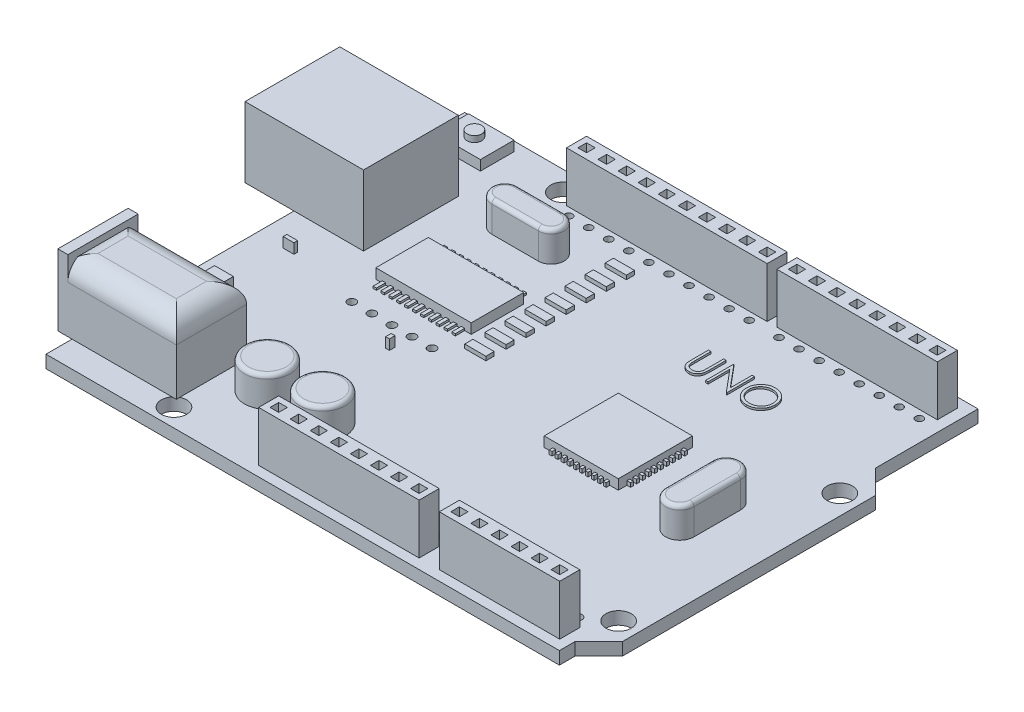
SolidWorks part; units mm, degrees
ref_plane "Front Plane" through (0, 0, 0) normal (0, 0, 1) x (1, 0, 0)
ref_plane "Top Plane" through (0, 0, 0) normal (0, 1, 0) x (1, 0, 0)
ref_plane "Right Plane" through (0, 0, 0) normal (1, 0, 0) x (0, 0, -1)
sketch "Sketch2" plane through (0, 0, 0) normal (0, 1, 0) x (1, 0, 0)
  line L0 (0, 0) -> (65, 0)
  line L1 (0, 0) -> (0, -53)
  line L2 (65, 0) -> (65, -13)
  line L3 (0, -53) -> (65, -53)
  line L4 (65, -13) -> (68, -16)
  line L5 (68, -16) -> (68, -48)
  line L6 (68, -48) -> (65, -51)
  line L7 (65, -51) -> (65, -53)
  circle A0 centre (15, -2.5) radius 1.6
  circle A1 centre (65.5, -18) radius 1.6
  circle A2 centre (65.5, -46) radius 1.6
  circle A3 centre (13.9, -50.7) radius 1.6
  dimension "D8" = 3.2
  dimension "D9" = 15
  dimension "D12" = 35
  dimension "D13" = 50.5
  dimension "D14" = 1.1
  dimension "D15" = 4.7
  dimension "D1" = 65
  dimension "D2" = 53
  dimension "D3" = 37
  dimension "D4" = 40
  dimension "D5" = 2
  dimension "D6" = 5
  dimension "D7" = 68
  dimension "D10" = 65.5
  dimension "D11" = 7
extrude "Boss-Extrude1" add sketch "Sketch2" along normal blind 1.6
sketch "Sketch3" plane through (0, 1.6, 0) normal (0, 1, 0) x (1, 0, 0)
  line L0 (-6.2, -9.6) -> (8.8, -9.6)
  line L1 (-6.2, -9.6) -> (-6.2, -21.6)
  line L2 (8.8, -9.6) -> (8.8, -21.6)
  line L3 (-6.2, -21.6) -> (8.8, -21.6)
  line L4 (65, 0) -> (0, 0) construction
  line L5 (0, 0) -> (0, -53) construction
  dimension "D1" = 9.6
  dimension "D2" = 12
  dimension "D3" = 15
  dimension "D4" = 6.2
extrude "Boss-Extrude2" add sketch "Sketch3" along normal blind 8.9
sketch "Sketch5" plane through (0, 1.6, 0) normal (0, 1, 0) x (1, 0, 0)
  line L0 (0, 0) -> (0, -9.6) construction
  line L1 (7.4283, -5.4315) -> (1.6434, -5.4315)
  line L2 (7.4283, -5.4315) -> (7.4283, -1.1571)
  line L3 (7.4283, -1.1571) -> (1.6434, -1.1571)
  line L4 (1.6434, -5.4315) -> (1.6434, -1.1571)
  line L5 (7.4283, -5.4315) -> (1.6434, -1.1571) construction
  line L6 (7.4283, -1.1571) -> (1.6434, -5.4315) construction
  line L7 (65, 0) -> (0, 0) construction
  point P0 (4.5358, -3.2943)
  dimension "D1" = 4.2744
  dimension "D2" = 5.7848
  dimension "D3" = 1.6434
  dimension "D4" = 1.1571
extrude "Boss-Extrude3" add sketch "Sketch5" along normal blind 1.27
sketch "Sketch6" plane through (0, 2.87, 0) normal (0, 1, 0) x (1, 0, 0)
  line L0 (1.6434, -1.1571) -> (7.4283, -5.4315) construction
  circle A0 centre (4.5358, -3.2943) radius 0.9278
  dimension "D1" = 1.8555
extrude "Boss-Extrude4" add sketch "Sketch6" along normal blind 0.762
sketch "Sketch7" plane through (0, 1.6, 0) normal (0, 1, 0) x (1, 0, 0)
  line L0 (0, -21.6) -> (0, -53) construction
  line L1 (-1.8, -40.8) -> (13.2, -40.8)
  line L2 (-1.8, -40.8) -> (-1.8, -49.7)
  line L3 (-1.8, -49.7) -> (13.2, -49.7)
  line L4 (13.2, -40.8) -> (13.2, -49.7)
  line L5 (-1.8, -40.8) -> (13.2, -49.7) construction
  line L6 (-1.8, -49.7) -> (13.2, -40.8) construction
  line L7 (0, -53) -> (65, -53) construction
  point P0 (5.7, -45.25)
  dimension "D1" = 8.9
  dimension "D2" = 1.8
  dimension "D3" = 15
  dimension "D4" = 3.3
extrude "Boss-Extrude5" add sketch "Sketch7" along normal blind 8.5
fillet "Fillet1" radius 2.54 4 edges at (5.7, 10.1, 49.7) (-1.8, 10.1, 45.25) (5.7, 10.1, 40.8) (13.2, 10.1, 45.25)
sketch "Sketch8" plane through (-1.8, 0, 0) normal (-1, 0, 0) x (0, 0, 1)
  line L0 (49.7, 1.6) -> (53, 1.6) construction
  line L1 (49.7, 1.6) -> (40.8, 1.6)
  line L2 (49.7, 1.6) -> (49.7, 10.6)
  line L3 (49.7, 10.6) -> (40.8, 10.6)
  line L4 (40.8, 1.6) -> (40.8, 10.6)
  line L5 (49.7, 1.6) -> (40.8, 10.6) construction
  line L6 (49.7, 10.6) -> (40.8, 1.6) construction
  line L7 (49.7, 7.56) -> (49.7, 1.6) construction
  line L9 (40.8, 7.56) -> (40.8, 1.6) construction
  point P0 (45.25, 6.1)
  dimension "D1" = 9
extrude "Boss-Extrude6" add sketch "Sketch8" against normal blind 1.27
sketch "Sketch9" plane through (-1.8, 0, 0) normal (-1, 0, 0) x (0, 0, 1)
  line L0 (45.25, 10.6) -> (45.25, 1.6) construction
  line L1 (49.7, 10.6) -> (40.8, 10.6) construction
  line L2 (40.8, 1.6) -> (49.7, 1.6) construction
  circle A0 centre (45.25, 6.1) radius 3
  dimension "D1" = 6
extrude "Cut-Extrude2" cut sketch "Sketch9" against normal blind 8.89
sketch "Sketch11" plane through (0, 1.6, 0) normal (0, 1, 0) x (1, 0, 0)
  line L0 (15.083, -10) -> (20.9573, -10) construction
  line L1 (15.083, -8.3682) -> (20.9573, -8.3682)
  line L2 (15.083, -11.6318) -> (20.9573, -11.6318)
  line L3 (59.2606, -32.0122) -> (59.2606, -26.1378) construction
  line L4 (57.4656, -32.0122) -> (57.4656, -26.1378)
  line L5 (61.0555, -32.0122) -> (61.0555, -26.1378)
  line L6 (0, -53) -> (65, -53) construction
  line L7 (0, -21.6) -> (0, -40.8) construction
  line L8 (65, 0) -> (0, 0) construction
  circle A0 centre (18.0202, -43) radius 2.8915
  circle A1 centre (25.0202, -43) radius 2.8915
  arc A2 (15.083, -8.3682) -> (15.083, -11.6318) centre (15.083, -10) ccw
  arc A3 (20.9573, -11.6318) -> (20.9573, -8.3682) centre (20.9573, -10) ccw
  arc A4 (57.4656, -32.0122) -> (61.0555, -32.0122) centre (59.2606, -32.0122) ccw
  arc A5 (61.0555, -26.1378) -> (57.4656, -26.1378) centre (59.2606, -26.1378) ccw
  point P6 (18.0202, -10)
  point P11 (59.2606, -29.075)
  dimension "D1" = 7
  dimension "D2" = 5.783
  dimension "D4" = 18.0202
  dimension "D6" = 1.6318
  dimension "14" = 10
  dimension "D5" = 5.8744
  dimension "D7" = 10
  dimension "D8" = 18.0202
extrude "Boss-Extrude8" add sketch "Sketch11" along normal blind 3.81
fillet "Fillet2" radius 0.508 1 edges at (18.0202, 5.41, 45.8915)
fillet "Fillet3" radius 0.508 9 edges at (59.2606, 5.41, 24.3429) (61.0555, 5.41, 29.075) (59.2606, 5.41, 33.8071) (18.0202, 5.41, 8.3682) (22.5891, 5.41, 10) (18.0202, 5.41, 11.6318) (57.4656, 5.41, 29.075) (13.4512, 5.41, 10) (25.0202, 5.41, 45.8915)
sketch "Sketch12" plane through (0, 1.6, 0) normal (0, 1, 0) x (1, 0, 0)
  line L0 (39.53, -1.23) -> (39.53, -3.77) construction
  line L1 (16.67, -1.23) -> (42.07, -1.23)
  line L2 (16.67, -1.23) -> (16.67, -3.77)
  line L3 (16.67, -3.77) -> (42.07, -3.77)
  line L4 (42.07, -1.23) -> (42.07, -3.77)
  line L5 (16.67, -1.23) -> (42.07, -3.77) construction
  line L6 (16.67, -3.77) -> (42.07, -1.23) construction
  line L7 (43.3, -1.23) -> (63.62, -1.23)
  line L8 (43.3, -1.23) -> (43.3, -3.77)
  line L9 (43.3, -3.77) -> (63.62, -3.77)
  line L10 (63.62, -1.23) -> (63.62, -3.77)
  line L11 (43.3, -1.23) -> (63.62, -3.77) construction
  line L12 (43.3, -3.77) -> (63.62, -1.23) construction
  line L13 (39.53, -1.23) -> (42.07, -3.77) construction
  line L14 (0, 0) -> (0, -9.6) construction
  line L15 (16.67, -2.5) -> (15, -2.5) construction
  line L17 (25.65, -49.19) -> (45.97, -49.19)
  line L18 (25.65, -49.19) -> (25.65, -51.73)
  line L19 (25.65, -51.73) -> (45.97, -51.73)
  line L20 (45.97, -49.19) -> (45.97, -51.73)
  line L21 (48.53, -49.19) -> (63.77, -49.19)
  line L22 (48.53, -49.19) -> (48.53, -51.73)
  line L23 (48.53, -51.73) -> (63.77, -51.73)
  line L24 (63.77, -49.19) -> (63.77, -51.73)
  line L25 (43.43, -49.19) -> (43.43, -51.73) construction
  line L26 (43.43, -51.73) -> (45.97, -49.19) construction
  line L27 (0, -49.7) -> (0, -53) construction
  line L28 (0, -53) -> (65, -53) construction
  line L29 (63.77, -49.19) -> (61.23, -51.73) construction
  line L30 (63.62, -1.23) -> (61.38, -3.77) construction
  circle A0 centre (15, -2.5) radius 1.6 construction
  point P0 (29.37, -2.5)
  point P5 (53.46, -2.5)
  point P14 (40.8, -2.5)
  point P27 (45.97, -50.46)
  point P28 (44.7, -50.46)
  point P35 (62.5, -50.46)
  point P37 (62.5, -2.5)
  dimension "D1" = 25.4
  dimension "D2" = 2.54
  dimension "D3" = 2.54
  dimension "D4" = 40.8
  dimension "D5" = 20.32
  dimension "D6" = 2.54
  dimension "D7" = 44.7
  dimension "D8" = 2.54
  dimension "D9" = 2.54
  dimension "D10" = 62.5
  dimension "D11" = 2.24
  dimension "D12" = 62.5
  dimension "D13" = 20.32
  dimension "D14" = 15.24
extrude "Boss-Extrude9" add sketch "Sketch12" along normal blind 6.35
sketch "Sketch13" plane through (0, 7.95, 0) normal (0, 1, 0) x (1, 0, 0)
  line L0 (19.9337, -3.0463) -> (19.9337, -1.9537)
  line L1 (18.4863, -3.0463) -> (17.3937, -3.0463)
  line L2 (18.4863, -3.0463) -> (18.4863, -1.9537)
  line L3 (18.4863, -1.9537) -> (17.3937, -1.9537)
  line L4 (17.3937, -3.0463) -> (17.3937, -1.9537)
  line L5 (18.4863, -3.0463) -> (17.3937, -1.9537) construction
  line L6 (18.4863, -1.9537) -> (17.3937, -3.0463) construction
  line L7 (21.0263, -1.9537) -> (19.9337, -1.9537)
  line L8 (21.0263, -3.0463) -> (19.9337, -3.0463)
  line L9 (21.0263, -3.0463) -> (21.0263, -1.9537)
  line L10 (22.4737, -3.0463) -> (22.4737, -1.9537)
  line L11 (23.5663, -1.9537) -> (22.4737, -1.9537)
  line L12 (23.5663, -3.0463) -> (22.4737, -3.0463)
  line L13 (23.5663, -3.0463) -> (23.5663, -1.9537)
  line L14 (25.0137, -3.0463) -> (25.0137, -1.9537)
  line L15 (26.1063, -1.9537) -> (25.0137, -1.9537)
  line L16 (26.1063, -3.0463) -> (25.0137, -3.0463)
  line L17 (26.1063, -3.0463) -> (26.1063, -1.9537)
  line L18 (27.5537, -3.0463) -> (27.5537, -1.9537)
  line L19 (28.6463, -1.9537) -> (27.5537, -1.9537)
  line L20 (28.6463, -3.0463) -> (27.5537, -3.0463)
  line L21 (28.6463, -3.0463) -> (28.6463, -1.9537)
  line L22 (30.0937, -3.0463) -> (30.0937, -1.9537)
  line L23 (31.1863, -1.9537) -> (30.0937, -1.9537)
  line L24 (31.1863, -3.0463) -> (30.0937, -3.0463)
  line L25 (31.1863, -3.0463) -> (31.1863, -1.9537)
  line L26 (32.6337, -3.0463) -> (32.6337, -1.9537)
  line L27 (33.7263, -1.9537) -> (32.6337, -1.9537)
  line L28 (33.7263, -3.0463) -> (32.6337, -3.0463)
  line L29 (33.7263, -3.0463) -> (33.7263, -1.9537)
  line L30 (35.1737, -3.0463) -> (35.1737, -1.9537)
  line L31 (36.2663, -1.9537) -> (35.1737, -1.9537)
  line L32 (36.2663, -3.0463) -> (35.1737, -3.0463)
  line L33 (36.2663, -3.0463) -> (36.2663, -1.9537)
  line L34 (16.67, -2.5) -> (17.94, -2.5) construction
  line L35 (16.67, -1.23) -> (16.67, -3.77) construction
  line L36 (42.07, -1.23) -> (43.3, -1.23) construction
  line L37 (43.3, -1.23) -> (42.685, -1.23) construction
  line L38 (42.685, -1.23) -> (42.685, 0) construction
  line L39 (65, 0) -> (0, 0) construction
  line L40 (44.0237, -3.0463) -> (44.0237, -1.9537)
  line L41 (44.0237, -3.0463) -> (45.1163, -3.0463)
  line L42 (44.0237, -1.9537) -> (45.1163, -1.9537)
  line L43 (49.1037, -3.0463) -> (49.1037, -1.9537)
  line L44 (49.1037, -3.0463) -> (50.1963, -3.0463)
  line L45 (49.1037, -1.9537) -> (50.1963, -1.9537)
  line L46 (50.1963, -3.0463) -> (50.1963, -1.9537)
  line L47 (51.6437, -3.0463) -> (51.6437, -1.9537)
  line L48 (51.6437, -3.0463) -> (52.7363, -3.0463)
  line L49 (51.6437, -1.9537) -> (52.7363, -1.9537)
  line L50 (52.7363, -3.0463) -> (52.7363, -1.9537)
  line L51 (54.1837, -3.0463) -> (54.1837, -1.9537)
  line L52 (54.1837, -3.0463) -> (55.2763, -3.0463)
  line L53 (54.1837, -1.9537) -> (55.2763, -1.9537)
  line L54 (55.2763, -3.0463) -> (55.2763, -1.9537)
  line L55 (56.7237, -3.0463) -> (56.7237, -1.9537)
  line L56 (56.7237, -3.0463) -> (57.8163, -3.0463)
  line L57 (56.7237, -1.9537) -> (57.8163, -1.9537)
  line L58 (57.8163, -3.0463) -> (57.8163, -1.9537)
  line L59 (59.2637, -3.0463) -> (59.2637, -1.9537)
  line L60 (59.2637, -3.0463) -> (60.3563, -3.0463)
  line L61 (59.2637, -1.9537) -> (60.3563, -1.9537)
  line L62 (60.3563, -3.0463) -> (60.3563, -1.9537)
  line L63 (61.8037, -3.0463) -> (61.8037, -1.9537)
  line L64 (61.8037, -3.0463) -> (62.8963, -3.0463)
  line L65 (61.8037, -1.9537) -> (62.8963, -1.9537)
  line L66 (62.8963, -3.0463) -> (62.8963, -1.9537)
  line L67 (45.1163, -3.0463) -> (45.1163, -1.9537)
  line L68 (46.5637, -3.0463) -> (46.5637, -1.9537)
  line L69 (46.5637, -3.0463) -> (47.6563, -3.0463)
  line L71 (46.5637, -1.9537) -> (47.6563, -1.9537)
  line L72 (47.6563, -3.0463) -> (47.6563, -1.9537)
  line L73 (41.6137, -49.9137) -> (42.7063, -49.9137)
  line L74 (41.6137, -49.9137) -> (41.6137, -51.0063)
  line L75 (41.6137, -51.0063) -> (42.7063, -51.0063)
  line L77 (26.3737, -49.9137) -> (27.4663, -49.9137)
  line L78 (26.3737, -49.9137) -> (26.3737, -51.0063)
  line L79 (26.3737, -51.0063) -> (27.4663, -51.0063)
  line L80 (27.4663, -49.9137) -> (27.4663, -51.0063)
  line L81 (26.3737, -50.46) -> (25.65, -50.46) construction
  line L82 (25.65, -49.19) -> (25.65, -51.73) construction
  line L83 (28.9137, -49.9137) -> (30.0063, -49.9137)
  line L84 (28.9137, -49.9137) -> (28.9137, -51.0063)
  line L85 (28.9137, -51.0063) -> (30.0063, -51.0063)
  line L86 (30.0063, -49.9137) -> (30.0063, -51.0063)
  line L87 (31.4537, -49.9137) -> (32.5463, -49.9137)
  line L88 (31.4537, -49.9137) -> (31.4537, -51.0063)
  line L89 (31.4537, -51.0063) -> (32.5463, -51.0063)
  line L90 (32.5463, -49.9137) -> (32.5463, -51.0063)
  line L91 (33.9937, -49.9137) -> (35.0863, -49.9137)
  line L92 (33.9937, -49.9137) -> (33.9937, -51.0063)
  line L93 (33.9937, -51.0063) -> (35.0863, -51.0063)
  line L94 (35.0863, -49.9137) -> (35.0863, -51.0063)
  line L95 (36.5337, -49.9137) -> (37.6263, -49.9137)
  line L96 (36.5337, -49.9137) -> (36.5337, -51.0063)
  line L97 (36.5337, -51.0063) -> (37.6263, -51.0063)
  line L98 (37.6263, -49.9137) -> (37.6263, -51.0063)
  line L99 (39.0737, -49.9137) -> (40.1663, -49.9137)
  line L100 (39.0737, -49.9137) -> (39.0737, -51.0063)
  line L101 (39.0737, -51.0063) -> (40.1663, -51.0063)
  line L102 (40.1663, -49.9137) -> (40.1663, -51.0063)
  line L103 (45.97, -51.73) -> (48.53, -51.73) construction
  line L104 (48.53, -51.73) -> (47.25, -51.73) construction
  line L105 (47.25, -51.73) -> (47.25, -53) construction
  line L106 (0, -53) -> (65, -53) construction
  line L107 (49.2537, -49.9137) -> (49.2537, -51.0063)
  line L108 (54.3337, -49.9137) -> (54.3337, -51.0063)
  line L109 (55.4263, -51.0063) -> (54.3337, -51.0063)
  line L110 (55.4263, -49.9137) -> (55.4263, -51.0063)
  line L111 (55.4263, -49.9137) -> (54.3337, -49.9137)
  line L112 (56.8737, -49.9137) -> (56.8737, -51.0063)
  line L113 (57.9663, -51.0063) -> (56.8737, -51.0063)
  line L114 (57.9663, -49.9137) -> (57.9663, -51.0063)
  line L115 (57.9663, -49.9137) -> (56.8737, -49.9137)
  line L116 (59.4137, -49.9137) -> (59.4137, -51.0063)
  line L117 (60.5063, -51.0063) -> (59.4137, -51.0063)
  line L118 (60.5063, -49.9137) -> (60.5063, -51.0063)
  line L119 (60.5063, -49.9137) -> (59.4137, -49.9137)
  line L120 (61.9537, -49.9137) -> (61.9537, -51.0063)
  line L121 (63.0463, -51.0063) -> (61.9537, -51.0063)
  line L122 (63.0463, -49.9137) -> (63.0463, -51.0063)
  line L123 (63.0463, -49.9137) -> (61.9537, -49.9137)
  line L124 (50.3463, -51.0063) -> (49.2537, -51.0063)
  line L125 (50.3463, -49.9137) -> (50.3463, -51.0063)
  line L126 (50.3463, -49.9137) -> (49.2537, -49.9137)
  line L127 (51.7937, -49.9137) -> (51.7937, -51.0063)
  line L128 (52.8863, -51.0063) -> (51.7937, -51.0063)
  line L129 (52.8863, -49.9137) -> (52.8863, -51.0063)
  line L130 (52.8863, -49.9137) -> (51.7937, -49.9137)
  line L132 (37.7137, -3.0463) -> (37.7137, -1.9537)
  line L133 (38.8063, -1.9537) -> (37.7137, -1.9537)
  line L134 (38.8063, -3.0463) -> (37.7137, -3.0463)
  line L135 (38.8063, -3.0463) -> (38.8063, -1.9537)
  line L136 (40.2537, -3.0463) -> (40.2537, -1.9537)
  line L137 (41.3463, -1.9537) -> (40.2537, -1.9537)
  line L138 (41.3463, -3.0463) -> (40.2537, -3.0463)
  line L139 (41.3463, -3.0463) -> (41.3463, -1.9537)
  line L140 (42.7063, -49.9137) -> (42.7063, -51.0063)
  line L141 (44.1537, -49.9137) -> (45.2463, -49.9137)
  line L142 (44.1537, -49.9137) -> (44.1537, -51.0063)
  line L143 (44.1537, -51.0063) -> (45.2463, -51.0063)
  line L144 (45.2463, -49.9137) -> (45.2463, -51.0063)
  point P0 (17.94, -2.5)
  point P84 (26.92, -51.0063)
  dimension "D2" = 2.54
  dimension "D3" = 1.0927
  dimension "D4" = 1.27
  dimension "D5" = 1.27
  dimension "D6" = 8
  dimension "D7" = 2.54
  dimension "D1" = 10
extrude "Cut-Extrude3" cut sketch "Sketch13" against normal blind 3.81
sketch "Sketch15" plane through (0, 1.6, 0) normal (0, 1, 0) x (1, 0, 0)
  line L0 (0, -53) -> (65, -53) construction
  line L1 (51.1538, -31.6917) -> (41.7703, -31.6917)
  line L2 (51.1538, -31.6917) -> (51.1538, -22.3083)
  line L3 (51.1538, -22.3083) -> (41.7703, -22.3083)
  line L4 (41.7703, -31.6917) -> (41.7703, -22.3083)
  line L5 (51.1538, -31.6917) -> (41.7703, -22.3083) construction
  line L6 (51.1538, -22.3083) -> (41.7703, -31.6917) construction
  line L7 (4.7493, -26.358) -> (3.3785, -26.358)
  line L8 (4.7493, -26.358) -> (4.7493, -25.8868)
  line L9 (4.7493, -25.8868) -> (3.3785, -25.8868)
  line L10 (3.3785, -26.358) -> (3.3785, -25.8868)
  line L11 (4.7493, -26.358) -> (3.3785, -25.8868) construction
  line L12 (4.7493, -25.8868) -> (3.3785, -26.358) construction
  line L13 (21.3282, -30.8535) -> (20.8488, -30.8535)
  line L14 (21.3282, -30.8535) -> (21.3282, -30.1486)
  line L15 (21.3282, -30.1486) -> (20.8488, -30.1486)
  line L16 (20.8488, -30.8535) -> (20.8488, -30.1486)
  line L17 (21.3282, -30.8535) -> (20.8488, -30.1486) construction
  line L18 (21.3282, -30.1486) -> (20.8488, -30.8535) construction
  line L19 (4.6108, -37.8097) -> (2.2268, -37.8097)
  line L20 (4.6108, -37.8097) -> (4.6108, -33.8836)
  line L21 (4.6108, -33.8836) -> (2.2268, -33.8836)
  line L22 (2.2268, -37.8097) -> (2.2268, -33.8836)
  line L23 (4.6108, -37.8097) -> (2.2268, -33.8836) construction
  line L24 (4.6108, -33.8836) -> (2.2268, -37.8097) construction
  line L25 (24.7492, -23.9138) -> (12.6715, -23.9138)
  line L26 (24.7492, -23.9138) -> (24.7492, -17.271)
  line L27 (24.7492, -17.271) -> (12.6715, -17.271)
  line L28 (12.6715, -23.9138) -> (12.6715, -17.271)
  line L29 (24.7492, -23.9138) -> (12.6715, -17.271) construction
  line L30 (24.7492, -17.271) -> (12.6715, -23.9138) construction
  line L31 (68, -48) -> (68, -16) construction
  line L32 (0, -21.6) -> (0, -40.8) construction
  line L34 (65, 0) -> (0, 0) construction
  point P0 (46.4621, -27)
  point P5 (4.0639, -26.1224)
  point P10 (21.0885, -30.501)
  point P15 (3.4188, -35.8466)
  point P20 (18.7104, -20.5924)
  dimension "D1" = 9.3835
  dimension "D2" = 12.0778
  dimension "D3" = 6.6428
  dimension "D4" = 26
  dimension "D5" = 21.5379
  dimension "D6" = 18.7104
  dimension "D7" = 20.5924
extrude "Boss-Extrude10" add sketch "Sketch15" along normal blind 1.27
sketch "Sketch16" plane through (0, 1.6, 0) normal (0, 1, 0) x (1, 0, 0)
  line L0 (17.94, -3.0463) -> (17.94, -4.77) construction
  line L1 (17.3937, -3.0463) -> (18.4863, -3.0463) construction
  line L2 (16.67, -3.77) -> (42.07, -3.77) construction
  line L3 (40.8, -3.0463) -> (40.8, -4.77) construction
  line L4 (40.2537, -3.0463) -> (41.3463, -3.0463) construction
  line L5 (42.07, -1.23) -> (43.3, -1.23) construction
  line L6 (43.3, -1.23) -> (42.685, -1.23) construction
  line L7 (42.685, -1.23) -> (42.685, 0) construction
  line L8 (65, 0) -> (0, 0) construction
  line L9 (44.57, -3.0463) -> (44.57, -4.77) construction
  circle A0 centre (-9.9058, 11.1483) radius 1.2565
  circle A1 centre (30.64, -4.77) radius 0.4778
  circle A2 centre (33.18, -4.77) radius 0.4778
  circle A3 centre (17.94, -4.77) radius 0.4778
  circle A4 centre (20.48, -4.77) radius 0.4778
  circle A5 centre (23.02, -4.77) radius 0.4778
  circle A6 centre (25.56, -4.77) radius 0.4778
  circle A7 centre (28.1, -4.77) radius 0.4778
  circle A8 centre (35.72, -4.77) radius 0.4778
  circle A9 centre (38.26, -4.77) radius 0.4778
  circle A10 centre (40.8, -4.77) radius 0.4778
  circle A11 centre (44.57, -4.77) radius 0.4778
  circle A12 centre (47.11, -4.77) radius 0.4778
  circle A13 centre (49.65, -4.77) radius 0.4778
  circle A14 centre (57.27, -4.77) radius 0.4778
  circle A15 centre (59.81, -4.77) radius 0.4778
  circle A16 centre (62.35, -4.77) radius 0.4778
  circle A19 centre (52.19, -4.77) radius 0.4778
  circle A20 centre (54.73, -4.77) radius 0.4778
  dimension "D4" = 0.9556
  dimension "D2" = 2.54
  dimension "D3" = 1
  dimension "D1" = 10
extrude "Cut-Extrude5" cut sketch "Sketch16" against normal blind 3.81
sketch "Sketch17" plane through (0, 1.6, 0) normal (0, 1, 0) x (1, 0, 0)
  line L0 (28.5824, -23.3444) -> (25.9009, -22.3015) construction
  line L1 (28.5824, -25.8844) -> (25.9009, -25.8844)
  line L2 (28.5824, -25.8844) -> (28.5824, -24.8415)
  line L3 (28.5824, -24.8415) -> (25.9009, -24.8415)
  line L4 (25.9009, -25.8844) -> (25.9009, -24.8415)
  line L5 (28.5824, -25.8844) -> (25.9009, -24.8415) construction
  line L6 (28.5824, -24.8415) -> (25.9009, -25.8844) construction
  line L7 (28.5824, -22.3015) -> (25.9009, -23.3444) construction
  line L8 (28.5824, -23.3444) -> (28.5824, -22.3015)
  line L9 (28.5824, -23.3444) -> (25.9009, -23.3444)
  line L10 (25.9009, -23.3444) -> (25.9009, -22.3015)
  line L11 (28.5824, -22.3015) -> (25.9009, -22.3015)
  line L12 (28.5824, -20.8044) -> (25.9009, -19.7615) construction
  line L13 (28.5824, -19.7615) -> (25.9009, -20.8044) construction
  line L14 (28.5824, -20.8044) -> (28.5824, -19.7615)
  line L15 (28.5824, -20.8044) -> (25.9009, -20.8044)
  line L16 (25.9009, -20.8044) -> (25.9009, -19.7615)
  line L17 (28.5824, -19.7615) -> (25.9009, -19.7615)
  line L18 (28.5824, -18.2644) -> (25.9009, -17.2215) construction
  line L19 (28.5824, -17.2215) -> (25.9009, -18.2644) construction
  line L20 (28.5824, -18.2644) -> (28.5824, -17.2215)
  line L21 (28.5824, -18.2644) -> (25.9009, -18.2644)
  line L22 (25.9009, -18.2644) -> (25.9009, -17.2215)
  line L23 (28.5824, -17.2215) -> (25.9009, -17.2215)
  line L24 (28.5824, -15.7244) -> (25.9009, -14.6815) construction
  line L25 (28.5824, -14.6815) -> (25.9009, -15.7244) construction
  line L26 (28.5824, -15.7244) -> (28.5824, -14.6815)
  line L27 (28.5824, -15.7244) -> (25.9009, -15.7244)
  line L28 (25.9009, -15.7244) -> (25.9009, -14.6815)
  line L29 (28.5824, -14.6815) -> (25.9009, -14.6815)
  line L30 (28.5824, -13.1844) -> (25.9009, -12.1415) construction
  line L31 (28.5824, -12.1415) -> (25.9009, -13.1844) construction
  line L32 (28.5824, -13.1844) -> (28.5824, -12.1415)
  line L33 (28.5824, -13.1844) -> (25.9009, -13.1844)
  line L34 (25.9009, -13.1844) -> (25.9009, -12.1415)
  line L35 (28.5824, -12.1415) -> (25.9009, -12.1415)
  line L36 (28.5824, -10.6444) -> (25.9009, -9.6015) construction
  line L37 (28.5824, -9.6015) -> (25.9009, -10.6444) construction
  line L38 (28.5824, -10.6444) -> (28.5824, -9.6015)
  line L39 (28.5824, -10.6444) -> (25.9009, -10.6444)
  line L40 (25.9009, -10.6444) -> (25.9009, -9.6015)
  line L41 (28.5824, -9.6015) -> (25.9009, -9.6015)
  line L42 (28.5824, -8.1044) -> (25.9009, -7.0615) construction
  line L43 (28.5824, -7.0615) -> (25.9009, -8.1044) construction
  line L44 (28.5824, -8.1044) -> (28.5824, -7.0615)
  line L45 (28.5824, -8.1044) -> (25.9009, -8.1044)
  line L46 (25.9009, -8.1044) -> (25.9009, -7.0615)
  line L47 (28.5824, -7.0615) -> (25.9009, -7.0615)
  point P0 (27.2416, -25.363)
  point P6 (27.2416, -22.823)
  point P12 (27.2416, -20.283)
  point P17 (27.2416, -17.743)
  point P22 (27.2416, -15.203)
  point P27 (27.2416, -12.663)
  point P32 (27.2416, -10.123)
  point P37 (27.2416, -7.583)
  dimension "D2" = 1.0429
  dimension "D3" = 2.54
  dimension "D1" = 8
extrude "Boss-Extrude11" add sketch "Sketch17" along normal blind 0.508
sketch "Sketch18" plane through (0, 1.6, 0) normal (0, 1, 0) x (1, 0, 0)
  text T0 "UNO"
sketch "Sketch20" plane through (0, 1.6, 0) normal (0, 1, 0) x (1, 0, 0)
  line L0 (45.97, -49.19) -> (25.65, -49.19) construction
  line L1 (26.92, -48.19) -> (26.92, -49.9137) construction
  line L2 (27.4663, -49.9137) -> (26.3737, -49.9137) construction
  line L3 (45.97, -51.73) -> (48.53, -51.73) construction
  line L4 (48.53, -51.73) -> (47.25, -51.73) construction
  line L5 (47.25, -51.73) -> (47.25, -53) construction
  line L6 (0, -53) -> (65, -53) construction
  circle A0 centre (26.92, -48.19) radius 0.5676
  circle A1 centre (29.46, -48.19) radius 0.5676
  circle A2 centre (32, -48.19) radius 0.5676
  circle A3 centre (34.54, -48.19) radius 0.5676
  circle A4 centre (37.08, -48.19) radius 0.5676
  circle A5 centre (39.62, -48.19) radius 0.5676
  circle A6 centre (42.16, -48.19) radius 0.5676
  circle A7 centre (44.7, -48.19) radius 0.5676
  circle A8 centre (49.8, -48.19) radius 0.5676
  circle A9 centre (52.34, -48.19) radius 0.5676
  circle A10 centre (54.88, -48.19) radius 0.5676
  circle A11 centre (57.42, -48.19) radius 0.5676
  circle A12 centre (59.96, -48.19) radius 0.5676
  circle A13 centre (62.5, -48.19) radius 0.5676
  dimension "D1" = 8
  dimension "D2" = 1.1352
  dimension "D3" = 2.54
  dimension "D4" = 1
extrude "Cut-Extrude6" cut sketch "Sketch20" against normal blind 23.368
sketch "Sketch21" plane through (0, 1.6, 0) normal (0, 1, 0) x (1, 0, 0)
  line L0 (18.7104, -23.9138) -> (18.7104, -27.9138) construction
  line L1 (12.6715, -23.9138) -> (24.7492, -23.9138) construction
  circle A0 centre (13.6304, -27.9138) radius 0.5282
  circle A1 centre (16.1704, -27.9138) radius 0.5282
  circle A2 centre (18.7104, -27.9138) radius 0.5282
  circle A3 centre (21.2504, -27.9138) radius 0.5282
  circle A4 centre (23.7904, -27.9138) radius 0.5282
  dimension "D1" = 5
  dimension "D3" = 1.0565
  dimension "D2" = 2.54
  dimension "D4" = 4
extrude "Cut-Extrude7" cut sketch "Sketch21" against normal blind 13.208
sketch "Sketch22" plane through (0, 1.6, 0) normal (0, 1, 0) x (1, 0, 0)
  line L0 (41.7703, -31.6917) -> (51.1538, -31.6917) construction
  line L1 (42.857, -31.2344) -> (43.2091, -31.2344)
  line L2 (42.857, -31.2344) -> (42.857, -32.149)
  line L3 (42.857, -32.149) -> (43.2091, -32.149)
  line L4 (43.2091, -31.2344) -> (43.2091, -32.149)
  line L5 (42.857, -31.2344) -> (43.2091, -32.149) construction
  line L6 (42.857, -32.149) -> (43.2091, -31.2344) construction
  line L7 (43.619, -31.2344) -> (43.9711, -32.149) construction
  line L8 (43.619, -32.149) -> (43.9711, -31.2344) construction
  line L9 (43.619, -31.2344) -> (43.619, -32.149)
  line L10 (43.619, -31.2344) -> (43.9711, -31.2344)
  line L11 (43.9711, -31.2344) -> (43.9711, -32.149)
  line L12 (43.619, -32.149) -> (43.9711, -32.149)
  line L13 (44.381, -31.2344) -> (44.7331, -32.149) construction
  line L14 (44.381, -32.149) -> (44.7331, -31.2344) construction
  line L15 (44.381, -31.2344) -> (44.381, -32.149)
  line L16 (44.381, -31.2344) -> (44.7331, -31.2344)
  line L17 (44.7331, -31.2344) -> (44.7331, -32.149)
  line L18 (44.381, -32.149) -> (44.7331, -32.149)
  line L19 (45.143, -31.2344) -> (45.4951, -32.149) construction
  line L20 (45.143, -32.149) -> (45.4951, -31.2344) construction
  line L21 (45.143, -31.2344) -> (45.143, -32.149)
  line L22 (45.143, -31.2344) -> (45.4951, -31.2344)
  line L23 (45.4951, -31.2344) -> (45.4951, -32.149)
  line L24 (45.143, -32.149) -> (45.4951, -32.149)
  line L25 (45.905, -31.2344) -> (46.2571, -32.149) construction
  line L26 (45.905, -32.149) -> (46.2571, -31.2344) construction
  line L27 (45.905, -31.2344) -> (45.905, -32.149)
  line L28 (45.905, -31.2344) -> (46.2571, -31.2344)
  line L29 (46.2571, -31.2344) -> (46.2571, -32.149)
  line L30 (45.905, -32.149) -> (46.2571, -32.149)
  line L31 (46.667, -31.2344) -> (47.0191, -32.149) construction
  line L32 (46.667, -32.149) -> (47.0191, -31.2344) construction
  line L33 (46.667, -31.2344) -> (46.667, -32.149)
  line L34 (46.667, -31.2344) -> (47.0191, -31.2344)
  line L35 (47.0191, -31.2344) -> (47.0191, -32.149)
  line L36 (46.667, -32.149) -> (47.0191, -32.149)
  line L37 (47.429, -31.2344) -> (47.7811, -32.149) construction
  line L38 (47.429, -32.149) -> (47.7811, -31.2344) construction
  line L39 (47.429, -31.2344) -> (47.429, -32.149)
  line L40 (47.429, -31.2344) -> (47.7811, -31.2344)
  line L41 (47.7811, -31.2344) -> (47.7811, -32.149)
  line L42 (47.429, -32.149) -> (47.7811, -32.149)
  line L43 (48.191, -31.2344) -> (48.5431, -32.149) construction
  line L44 (48.191, -32.149) -> (48.5431, -31.2344) construction
  line L45 (48.191, -31.2344) -> (48.191, -32.149)
  line L46 (48.191, -31.2344) -> (48.5431, -31.2344)
  line L47 (48.5431, -31.2344) -> (48.5431, -32.149)
  line L48 (48.191, -32.149) -> (48.5431, -32.149)
  line L49 (48.953, -31.2344) -> (49.3051, -32.149) construction
  line L50 (48.953, -32.149) -> (49.3051, -31.2344) construction
  line L51 (48.953, -31.2344) -> (48.953, -32.149)
  line L52 (48.953, -31.2344) -> (49.3051, -31.2344)
  line L53 (49.3051, -31.2344) -> (49.3051, -32.149)
  line L54 (48.953, -32.149) -> (49.3051, -32.149)
  line L55 (49.715, -31.2344) -> (50.0671, -32.149) construction
  line L56 (49.715, -32.149) -> (50.0671, -31.2344) construction
  line L57 (49.715, -31.2344) -> (49.715, -32.149)
  line L58 (49.715, -31.2344) -> (50.0671, -31.2344)
  line L59 (50.0671, -31.2344) -> (50.0671, -32.149)
  line L60 (49.715, -32.149) -> (50.0671, -32.149)
  line L61 (46.4621, -31.6917) -> (46.4621, -22.3083) construction
  line L62 (41.7703, -31.6917) -> (51.1538, -31.6917) construction
  line L63 (51.1538, -22.3083) -> (41.7703, -22.3083) construction
  line L64 (46.4621, -27) -> (41.7703, -27) construction
  line L65 (41.7703, -22.3083) -> (41.7703, -31.6917) construction
  line L66 (42.2276, -23.3949) -> (42.2276, -23.7471)
  line L67 (42.2276, -23.3949) -> (41.313, -23.3949)
  line L68 (42.2276, -23.7471) -> (41.313, -23.7471)
  line L69 (41.313, -23.3949) -> (41.313, -23.7471)
  line L70 (42.2276, -24.1569) -> (41.313, -24.1569)
  line L71 (42.2276, -24.1569) -> (42.2276, -24.5091)
  line L72 (42.2276, -24.5091) -> (41.313, -24.5091)
  line L73 (42.2276, -24.9189) -> (42.2276, -25.2711)
  line L74 (42.2276, -25.2711) -> (41.313, -25.2711)
  line L75 (42.2276, -24.9189) -> (41.313, -24.9189)
  line L76 (41.313, -24.1569) -> (41.313, -24.5091)
  line L77 (41.313, -24.9189) -> (41.313, -25.2711)
  line L78 (42.2276, -25.6809) -> (42.2276, -26.0331)
  line L79 (42.2276, -25.6809) -> (41.313, -25.6809)
  line L80 (42.2276, -26.0331) -> (41.313, -26.0331)
  line L81 (41.313, -25.6809) -> (41.313, -26.0331)
  line L82 (42.2276, -26.4429) -> (41.313, -26.4429)
  line L83 (42.2276, -26.4429) -> (42.2276, -26.7951)
  line L84 (42.2276, -26.7951) -> (41.313, -26.7951)
  line L85 (42.2276, -27.2049) -> (41.313, -27.2049)
  line L86 (42.2276, -27.2049) -> (42.2276, -27.5571)
  line L87 (42.2276, -27.5571) -> (41.313, -27.5571)
  line L88 (41.313, -27.2049) -> (41.313, -27.5571)
  line L89 (41.313, -26.4429) -> (41.313, -26.7951)
  line L90 (42.2276, -27.9669) -> (42.2276, -28.3191)
  line L91 (42.2276, -27.9669) -> (41.313, -27.9669)
  line L92 (41.313, -27.9669) -> (41.313, -28.3191)
  line L93 (42.2276, -28.7289) -> (41.313, -28.7289)
  line L94 (42.2276, -28.3191) -> (41.313, -28.3191)
  line L95 (42.2276, -28.7289) -> (42.2276, -29.0811)
  line L96 (42.2276, -29.0811) -> (41.313, -29.0811)
  line L97 (41.313, -28.7289) -> (41.313, -29.0811)
  line L98 (42.2276, -29.4909) -> (42.2276, -29.8431)
  line L99 (42.2276, -29.4909) -> (41.313, -29.4909)
  line L100 (42.2276, -29.8431) -> (41.313, -29.8431)
  line L101 (41.313, -29.4909) -> (41.313, -29.8431)
  line L102 (42.2276, -30.2529) -> (41.313, -30.2529)
  line L103 (42.2276, -30.2529) -> (42.2276, -30.6051)
  line L104 (42.2276, -30.6051) -> (41.313, -30.6051)
  line L105 (41.313, -30.2529) -> (41.313, -30.6051)
  line L106 (50.0671, -22.7656) -> (49.715, -22.7656)
  line L107 (50.0671, -22.7656) -> (50.0671, -21.851)
  line L108 (49.715, -22.7656) -> (49.715, -21.851)
  line L109 (50.0671, -21.851) -> (49.715, -21.851)
  line L110 (49.3051, -22.7656) -> (49.3051, -21.851)
  line L111 (49.3051, -22.7656) -> (48.953, -22.7656)
  line L112 (48.953, -22.7656) -> (48.953, -21.851)
  line L113 (48.5431, -22.7656) -> (48.191, -22.7656)
  line L114 (48.191, -22.7656) -> (48.191, -21.851)
  line L115 (48.5431, -22.7656) -> (48.5431, -21.851)
  line L116 (49.3051, -21.851) -> (48.953, -21.851)
  line L117 (48.5431, -21.851) -> (48.191, -21.851)
  line L118 (47.7811, -22.7656) -> (47.429, -22.7656)
  line L119 (47.7811, -22.7656) -> (47.7811, -21.851)
  line L120 (47.429, -22.7656) -> (47.429, -21.851)
  line L121 (47.7811, -21.851) -> (47.429, -21.851)
  line L122 (47.0191, -22.7656) -> (47.0191, -21.851)
  line L123 (47.0191, -22.7656) -> (46.667, -22.7656)
  line L124 (46.667, -22.7656) -> (46.667, -21.851)
  line L125 (46.2571, -22.7656) -> (46.2571, -21.851)
  line L126 (46.2571, -22.7656) -> (45.905, -22.7656)
  line L127 (45.905, -22.7656) -> (45.905, -21.851)
  line L128 (46.2571, -21.851) -> (45.905, -21.851)
  line L129 (47.0191, -21.851) -> (46.667, -21.851)
  line L130 (45.4951, -22.7656) -> (45.143, -22.7656)
  line L131 (45.4951, -22.7656) -> (45.4951, -21.851)
  line L132 (45.4951, -21.851) -> (45.143, -21.851)
  line L133 (44.7331, -22.7656) -> (44.7331, -21.851)
  line L134 (45.143, -22.7656) -> (45.143, -21.851)
  line L135 (44.7331, -22.7656) -> (44.381, -22.7656)
  line L136 (44.381, -22.7656) -> (44.381, -21.851)
  line L137 (44.7331, -21.851) -> (44.381, -21.851)
  line L138 (43.9711, -22.7656) -> (43.619, -22.7656)
  line L139 (43.9711, -22.7656) -> (43.9711, -21.851)
  line L140 (43.619, -22.7656) -> (43.619, -21.851)
  line L141 (43.9711, -21.851) -> (43.619, -21.851)
  line L142 (43.2091, -22.7656) -> (43.2091, -21.851)
  line L143 (43.2091, -22.7656) -> (42.857, -22.7656)
  line L144 (42.857, -22.7656) -> (42.857, -21.851)
  line L145 (43.2091, -21.851) -> (42.857, -21.851)
  line L146 (50.6965, -30.6051) -> (50.6965, -30.2529)
  line L147 (50.6965, -30.6051) -> (51.6111, -30.6051)
  line L148 (50.6965, -30.2529) -> (51.6111, -30.2529)
  line L149 (51.6111, -30.6051) -> (51.6111, -30.2529)
  line L150 (50.6965, -29.8431) -> (51.6111, -29.8431)
  line L151 (50.6965, -29.8431) -> (50.6965, -29.4909)
  line L152 (50.6965, -29.4909) -> (51.6111, -29.4909)
  line L153 (50.6965, -29.0811) -> (50.6965, -28.7289)
  line L154 (50.6965, -28.7289) -> (51.6111, -28.7289)
  line L155 (50.6965, -29.0811) -> (51.6111, -29.0811)
  line L156 (51.6111, -29.8431) -> (51.6111, -29.4909)
  line L157 (51.6111, -29.0811) -> (51.6111, -28.7289)
  line L158 (50.6965, -28.3191) -> (50.6965, -27.9669)
  line L159 (50.6965, -28.3191) -> (51.6111, -28.3191)
  line L160 (50.6965, -27.9669) -> (51.6111, -27.9669)
  line L161 (51.6111, -28.3191) -> (51.6111, -27.9669)
  line L162 (50.6965, -27.5571) -> (51.6111, -27.5571)
  line L163 (50.6965, -27.5571) -> (50.6965, -27.2049)
  line L164 (50.6965, -27.2049) -> (51.6111, -27.2049)
  line L165 (50.6965, -26.7951) -> (51.6111, -26.7951)
  line L166 (50.6965, -26.7951) -> (50.6965, -26.4429)
  line L167 (50.6965, -26.4429) -> (51.6111, -26.4429)
  line L168 (51.6111, -26.7951) -> (51.6111, -26.4429)
  line L169 (51.6111, -27.5571) -> (51.6111, -27.2049)
  line L170 (50.6965, -26.0331) -> (50.6965, -25.6809)
  line L171 (50.6965, -26.0331) -> (51.6111, -26.0331)
  line L172 (51.6111, -26.0331) -> (51.6111, -25.6809)
  line L173 (50.6965, -25.2711) -> (51.6111, -25.2711)
  line L174 (50.6965, -25.6809) -> (51.6111, -25.6809)
  line L175 (50.6965, -25.2711) -> (50.6965, -24.9189)
  line L176 (50.6965, -24.9189) -> (51.6111, -24.9189)
  line L177 (51.6111, -25.2711) -> (51.6111, -24.9189)
  line L178 (50.6965, -24.5091) -> (50.6965, -24.1569)
  line L179 (50.6965, -24.5091) -> (51.6111, -24.5091)
  line L180 (50.6965, -24.1569) -> (51.6111, -24.1569)
  line L181 (51.6111, -24.5091) -> (51.6111, -24.1569)
  line L182 (50.6965, -23.7471) -> (51.6111, -23.7471)
  line L183 (50.6965, -23.7471) -> (50.6965, -23.3949)
  line L184 (50.6965, -23.3949) -> (51.6111, -23.3949)
  line L185 (51.6111, -23.7471) -> (51.6111, -23.3949)
  line L186 (42.857, -21.851) -> (43.2091, -22.7656) construction
  point P0 (43.0331, -31.6917)
  point P7 (43.0331, -22.3083)
  point P9 (43.7951, -31.6917)
  point P14 (44.5571, -31.6917)
  point P19 (45.3191, -31.6917)
  point P24 (46.0811, -31.6917)
  point P29 (46.8431, -31.6917)
  point P34 (47.6051, -31.6917)
  point P39 (48.3671, -31.6917)
  point P44 (49.1291, -31.6917)
  point P49 (49.8911, -31.6917)
  dimension "D1" = 10
  dimension "D2" = 0.3521
  dimension "D3" = 0.9146
  dimension "D4" = 0.762
  dimension "D5" = 4
extrude "Boss-Extrude12" add sketch "Sketch22" along normal blind 0.508
extrude "Boss-Extrude14" add sketch "Sketch18" along normal blind 0.254
sketch "Sketch25" plane through (0, 1.6, 0) normal (0, 1, 0) x (1, 0, 0)
  line L0 (14.4975, -25.0924) -> (14.4975, -16.0924)
  line L1 (13.9232, -25.0924) -> (13.4975, -25.0924)
  line L2 (13.9232, -25.0924) -> (13.9232, -16.0924)
  line L3 (13.9232, -16.0924) -> (13.4975, -16.0924)
  line L4 (13.4975, -25.0924) -> (13.4975, -16.0924)
  line L5 (13.9232, -25.0924) -> (13.4975, -16.0924) construction
  line L6 (13.9232, -16.0924) -> (13.4975, -25.0924) construction
  line L7 (14.9232, -16.0924) -> (14.4975, -16.0924)
  line L8 (14.9232, -25.0924) -> (14.9232, -16.0924)
  line L9 (14.9232, -25.0924) -> (14.4975, -25.0924)
  line L10 (15.4975, -25.0924) -> (15.4975, -16.0924)
  line L11 (15.9232, -16.0924) -> (15.4975, -16.0924)
  line L12 (15.9232, -25.0924) -> (15.9232, -16.0924)
  line L13 (15.9232, -25.0924) -> (15.4975, -25.0924)
  line L14 (16.4975, -25.0924) -> (16.4975, -16.0924)
  line L15 (16.9232, -16.0924) -> (16.4975, -16.0924)
  line L16 (16.9232, -25.0924) -> (16.9232, -16.0924)
  line L17 (16.9232, -25.0924) -> (16.4975, -25.0924)
  line L18 (17.4975, -25.0924) -> (17.4975, -16.0924)
  line L19 (17.9232, -16.0924) -> (17.4975, -16.0924)
  line L20 (17.9232, -25.0924) -> (17.9232, -16.0924)
  line L21 (17.9232, -25.0924) -> (17.4975, -25.0924)
  line L22 (18.4975, -25.0924) -> (18.4975, -16.0924)
  line L23 (18.9232, -16.0924) -> (18.4975, -16.0924)
  line L24 (18.9232, -25.0924) -> (18.9232, -16.0924)
  line L25 (18.9232, -25.0924) -> (18.4975, -25.0924)
  line L26 (19.4975, -25.0924) -> (19.4975, -16.0924)
  line L27 (19.9232, -16.0924) -> (19.4975, -16.0924)
  line L28 (19.9232, -25.0924) -> (19.9232, -16.0924)
  line L29 (19.9232, -25.0924) -> (19.4975, -25.0924)
  line L30 (20.4975, -25.0924) -> (20.4975, -16.0924)
  line L31 (20.9232, -16.0924) -> (20.4975, -16.0924)
  line L32 (20.9232, -25.0924) -> (20.9232, -16.0924)
  line L33 (20.9232, -25.0924) -> (20.4975, -25.0924)
  line L34 (21.4975, -25.0924) -> (21.4975, -16.0924)
  line L35 (21.9232, -16.0924) -> (21.4975, -16.0924)
  line L36 (21.9232, -25.0924) -> (21.9232, -16.0924)
  line L37 (21.9232, -25.0924) -> (21.4975, -25.0924)
  line L38 (22.4975, -25.0924) -> (22.4975, -16.0924)
  line L39 (22.9232, -16.0924) -> (22.4975, -16.0924)
  line L40 (22.9232, -25.0924) -> (22.9232, -16.0924)
  line L41 (22.9232, -25.0924) -> (22.4975, -25.0924)
  line L42 (23.4975, -25.0924) -> (23.4975, -16.0924)
  line L43 (23.9232, -16.0924) -> (23.4975, -16.0924)
  line L44 (23.9232, -25.0924) -> (23.9232, -16.0924)
  line L45 (23.9232, -25.0924) -> (23.4975, -25.0924)
  line L46 (12.6715, -20.5924) -> (13.4975, -20.5924) construction
  line L47 (12.6715, -17.271) -> (12.6715, -23.9138) construction
  line L48 (24.7492, -20.5924) -> (23.9232, -20.5924) construction
  line L49 (24.7492, -23.9138) -> (24.7492, -17.271) construction
  point P0 (13.7104, -20.5924)
  dimension "D1" = 11
  dimension "D2" = 9
  dimension "D3" = 0.4257
  dimension "D4" = 1
extrude "Boss-Extrude15" add sketch "Sketch25" along normal blind 0.254
sketch "Sketch26" plane through (-6.2, 0, 0) normal (-1, 0, 0) x (0, 0, 1)
  line L0 (10.6, 2.6) -> (10.6, 7.5)
  line L1 (10.6, 7.5) -> (12.6, 9.5)
  line L2 (12.6, 9.5) -> (18.6, 9.5)
  line L3 (18.6, 9.5) -> (20.6, 7.5)
  line L4 (20.6, 7.5) -> (20.6, 2.6)
  line L5 (20.6, 2.6) -> (10.6, 2.6)
  line L6 (15.6, 10.5) -> (15.6, 1.6) construction
  line L7 (13.6, 6.5) -> (17.6, 6.5)
  line L8 (13.6, 6.5) -> (13.6, 5)
  line L9 (13.6, 5) -> (17.6, 5)
  line L10 (17.6, 6.5) -> (17.6, 5)
  line L11 (9.6, 10.5) -> (21.6, 10.5) construction
  line L12 (9.6, 1.6) -> (21.6, 1.6) construction
  line L13 (9.6, 10.5) -> (9.6, 1.6) construction
  dimension "D1" = 1
  dimension "D2" = 1
  dimension "D3" = 6
  dimension "D4" = 1
  dimension "D5" = 45
  dimension "D6" = 1.5
  dimension "4" = 4
  dimension "D7" = 3
extrude "Cut-Extrude8" cut sketch "Sketch26" against normal blind 12
